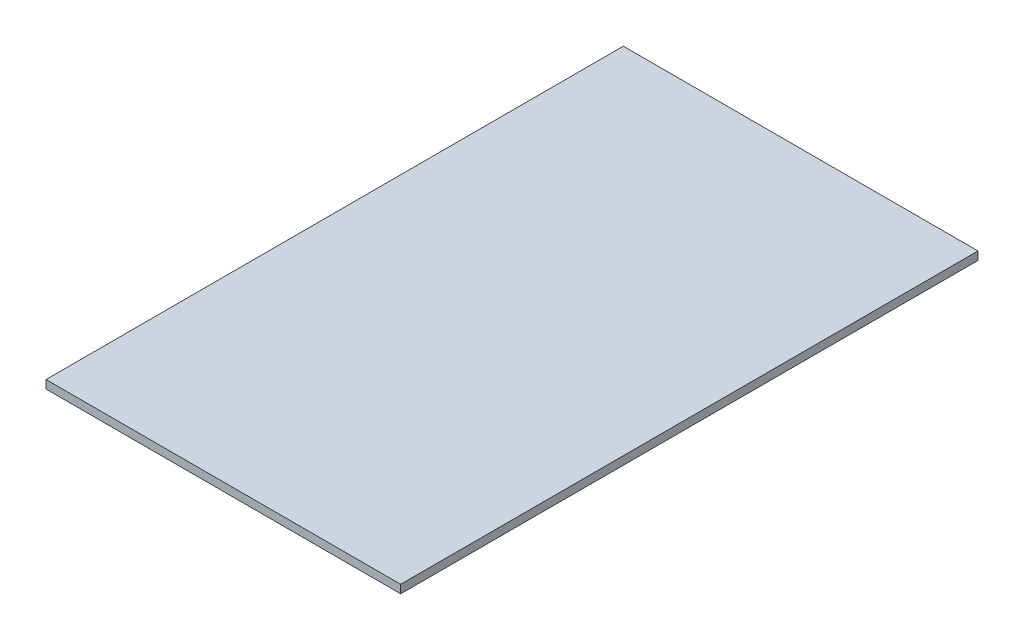
SolidWorks part; units mm, degrees
material "Acrylic (Medium-high impact)"
ref_plane "Front Plane" through (0, 0, 0) normal (0, 0, 1) x (1, 0, 0)
ref_plane "Top Plane" through (0, 0, 0) normal (0, 1, 0) x (1, 0, 0)
ref_plane "Right Plane" through (0, 0, 0) normal (1, 0, 0) x (0, 0, -1)
sketch "Sketch1" plane through (0, 0, 0) normal (0, 1, 0) x (1, 0, 0)
  line L1 (-2.2273, 2.8807) -> (134.2977, 2.8807)
  line L2 (-2.2273, 2.8807) -> (-2.2273, -219.3693)
  line L3 (-2.2273, -219.3693) -> (134.2977, -219.3693)
  line L4 (134.2977, 2.8807) -> (134.2977, -219.3693)
  dimension "D1" = 136.525
  dimension "D2" = 222.25
extrude "Boss-Extrude1" add sketch "Sketch1" along normal blind 3.175
